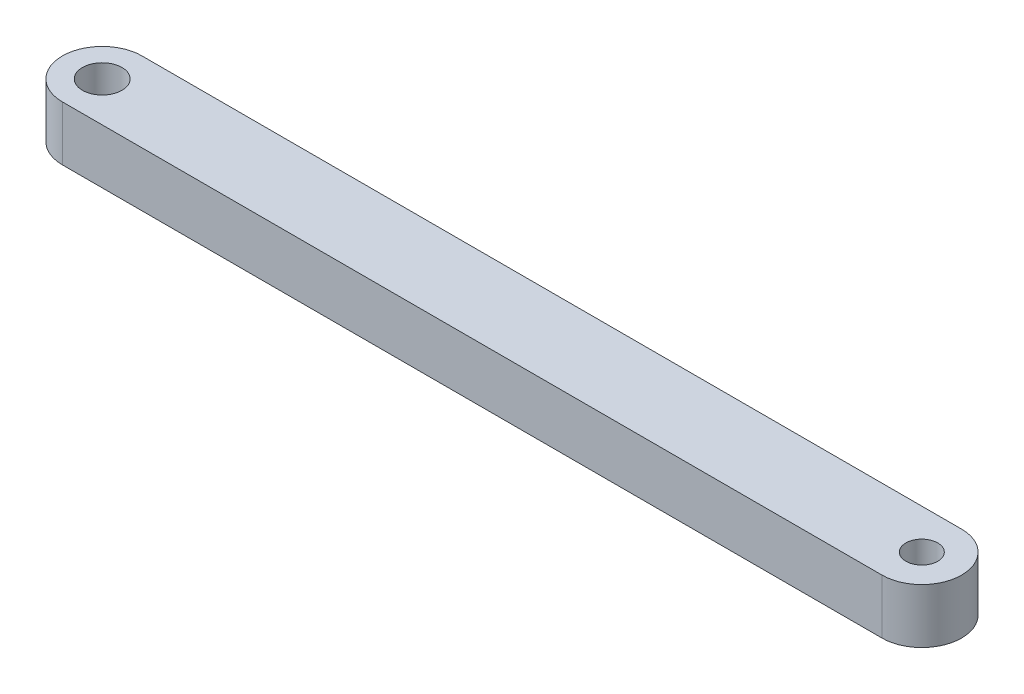
SolidWorks part; units mm, degrees
ref_plane "Front Plane" through (0, 0, 0) normal (0, 0, 1) x (1, 0, 0)
ref_plane "Top Plane" through (0, 0, 0) normal (0, 1, 0) x (1, 0, 0)
ref_plane "Right Plane" through (0, 0, 0) normal (1, 0, 0) x (0, 0, -1)
sketch "Sketch1" plane through (0, 0, 0) normal (0, 1, 0) x (1, 0, 0)
  line L0 (-22.225, 0) -> (22.225, 0) construction
  line L1 (-22.225, 2.159) -> (22.225, 2.159)
  line L2 (-22.225, -2.159) -> (22.225, -2.159)
  arc A0 (-22.225, 2.159) -> (-22.225, -2.159) centre (-22.225, 0) ccw
  arc A1 (22.225, -2.159) -> (22.225, 2.159) centre (22.225, 0) ccw
  circle A2 centre (22.225, 0) radius 0.8636
  circle A3 centre (-22.225, 0) radius 1.0731
  point P3 (0, 0)
  dimension "D1" = 1.7272
  dimension "D2" = 2.159
  dimension "D4" = 2.1463
  dimension "D3" = 44.45
extrude "Boss-Extrude1" add sketch "Sketch1" along normal blind 2.9591
